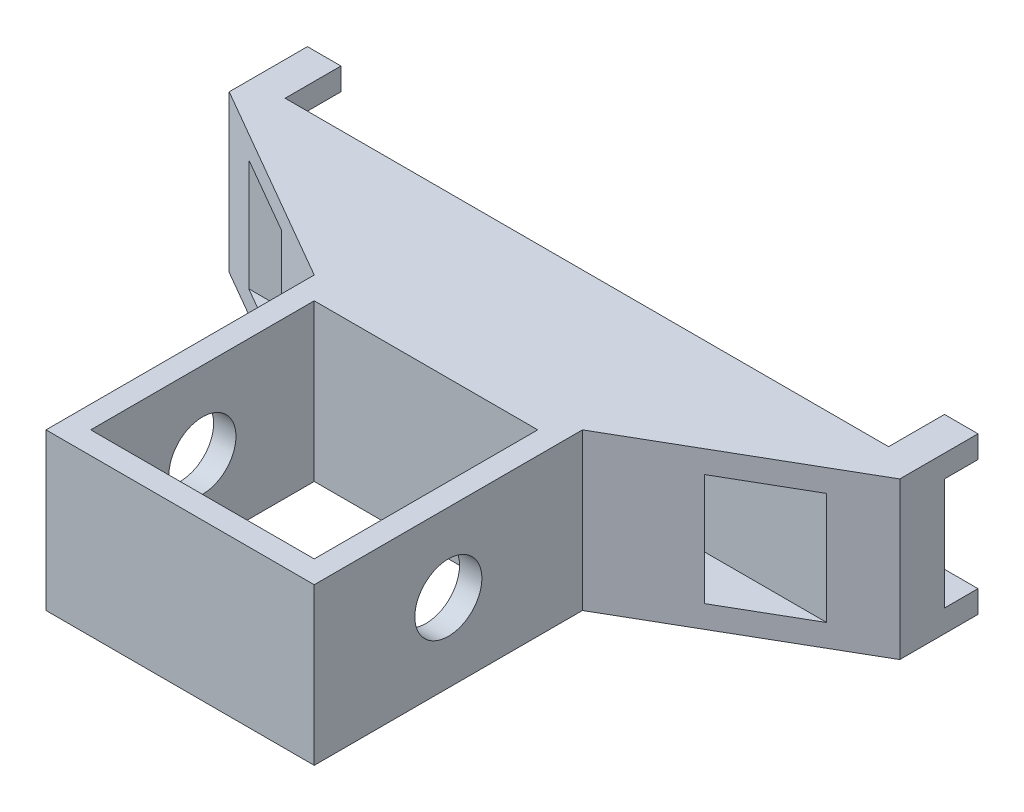
SolidWorks part; units mm, degrees
ref_plane "Front" through (0, 0, 0) normal (0, 0, 1) x (1, 0, 0)
ref_plane "Top" through (0, 0, 0) normal (0, 1, 0) x (1, 0, 0)
ref_plane "Right" through (0, 0, 0) normal (1, 0, 0) x (0, 0, -1)
sketch "Эскиз1" plane through (0, 0, 0) normal (0, 1, 0) x (1, 0, 0)
  line L0 (-6, 0) -> (6, 0)
  line L1 (6, 0) -> (6, 12)
  line L2 (6, 12) -> (-6, 12)
  line L3 (-6, 12) -> (-6, 0)
  line L4 (-6, 12) -> (-15, 17.1962)
  line L5 (-15, 17.1962) -> (-15, 20.6962)
  line L6 (-15, 20.6962) -> (15, 20.6962)
  line L7 (15, 20.6962) -> (15, 17.1962)
  line L8 (15, 17.1962) -> (6, 12)
  line L9 (0, 12) -> (0, 20.6962) construction
  dimension "D1" = 12
  dimension "D2" = 30
  dimension "D3" = 3.5
  dimension "D4" = 150
extrude "Бобышка-Вытянуть1" add sketch "Эскиз1" along normal blind 7 contours L2 L3 L0 L1 | L9 L2 L8 L7 L6 | L2 L9 L6 L5 L4
sketch "Эскиз2" plane through (0, 7, 0) normal (0, 1, 0) x (1, 0, 0)
  line L0 (-6, 0) -> (6, 0) construction
  line L1 (-5, 1) -> (5, 1)
  line L2 (-5, 1) -> (-5, 11)
  line L3 (-5, 11) -> (5, 11)
  line L4 (5, 1) -> (5, 11)
  line L5 (-6, 12) -> (-6, 0) construction
  dimension "D1" = 10
  dimension "D2" = 1
  dimension "D3" = 1
extrude "Вырез-Вытянуть1" cut sketch "Эскиз2" against normal through all
sketch "Эскиз4" plane through (-6, 0, 0) normal (-1, 0, 0) x (0, 0, 1)
  line L1 (-6, 0) -> (-6, 7) construction
  line L2 (-12, 0) -> (0, 0) construction
  line L3 (-12, 7) -> (0, 7) construction
  line L4 (0, 3.5) -> (-6, 3.5) construction
  line L5 (0, 7) -> (0, 0) construction
  circle A0 centre (-6, 3.5) radius 1.5
  dimension "D1" = 3
extrude "Вырез-Вытянуть2" cut sketch "Эскиз4" against normal through all
sketch "Эскиз5" plane through (0, 0, 0) normal (0, -1, 0) x (1, 0, 0)
  line L0 (-15, -20.6962) -> (15, -20.6962) construction
  line L1 (13.5, -20.6962) -> (-13.5, -20.6962)
  line L2 (13.5, -20.6962) -> (13.5, -18.1962)
  line L3 (13.5, -18.1962) -> (-13.5, -18.1962)
  line L4 (-13.5, -20.6962) -> (-13.5, -18.1962)
  line L5 (15, -20.6962) -> (15, -17.1962) construction
  line L6 (-15, -17.1962) -> (-15, -20.6962) construction
  dimension "D1" = 1.5
  dimension "D2" = 1.5
  dimension "D3" = 2.5
extrude "Вырез-Вытянуть3" cut sketch "Эскиз5" against normal through all
sketch "Эскиз6" plane through (15, 0, 0) normal (1, 0, 0) x (0, 0, -1)
  line L0 (17.1962, 7) -> (12, 7) construction
  line L1 (14, 6) -> (16, 6)
  line L2 (14, 6) -> (14, 1)
  line L3 (14, 1) -> (16, 1)
  line L4 (16, 6) -> (16, 1)
  line L5 (12, 7) -> (12, 0) construction
  dimension "D1" = 5
  dimension "D2" = 2
  dimension "D3" = 1
  dimension "D4" = 2
extrude "Вырез-Вытянуть4" cut sketch "Эскиз6" against normal through all
sketch "Эскиз7" plane through (-15, 0, 0) normal (-1, 0, 0) x (0, 0, 1)
  line L0 (-20.6962, 7) -> (-20.6962, 0) construction
  line L1 (-20.6962, 6) -> (-19.1962, 6)
  line L2 (-20.6962, 6) -> (-20.6962, 1)
  line L3 (-20.6962, 1) -> (-19.1962, 1)
  line L4 (-19.1962, 6) -> (-19.1962, 1)
  line L5 (-17.1962, 7) -> (-20.6962, 7) construction
  line L6 (-17.1962, 0) -> (-20.6962, 0) construction
  dimension "D1" = 1
  dimension "D2" = 1
  dimension "D3" = 1.5
extrude "Вырез-Вытянуть5" cut sketch "Эскиз7" against normal through all
